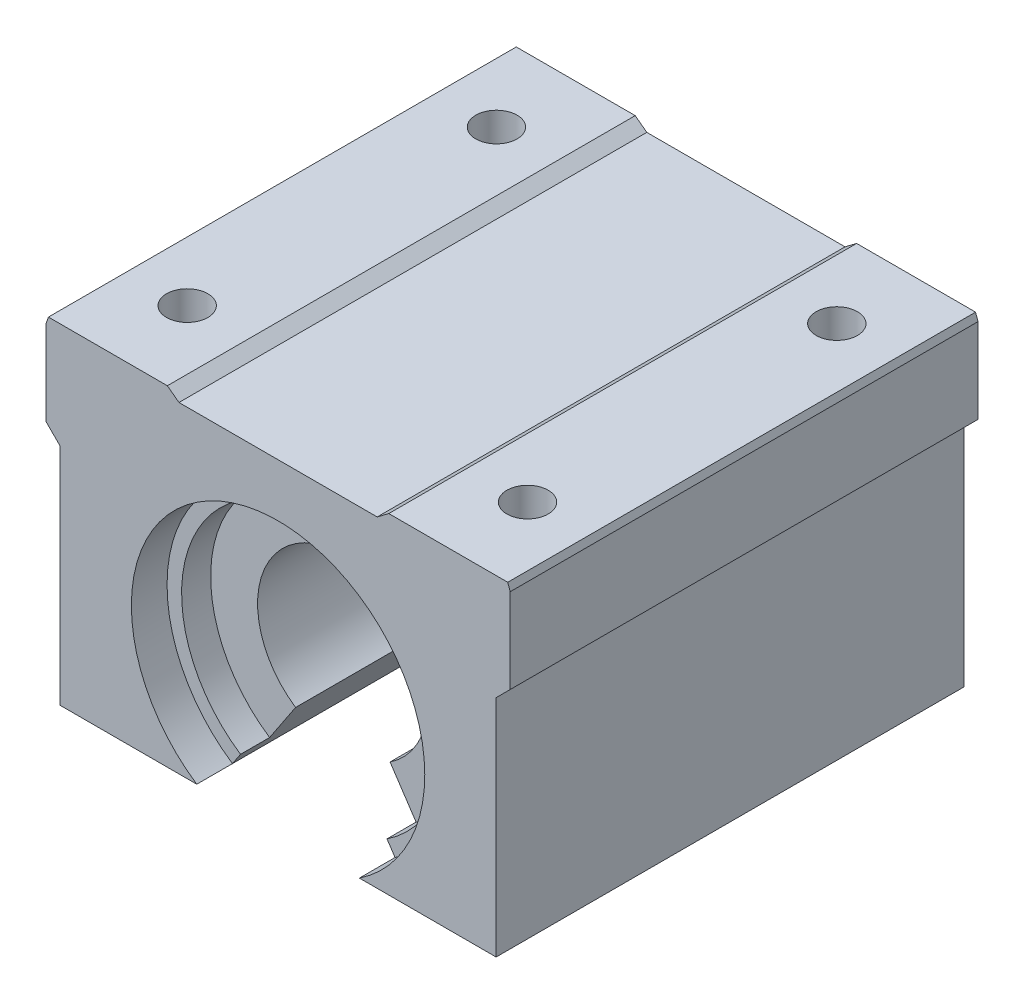
SolidWorks part; units mm, degrees
ref_plane "Front Plane" through (0, 0, 0) normal (0, 0, 1) x (1, 0, 0)
ref_plane "Top Plane" through (0, 0, 0) normal (0, 1, 0) x (1, 0, 0)
ref_plane "Right Plane" through (0, 0, 0) normal (1, 0, 0) x (0, 0, -1)
sketch "Sketch2" plane through (0, 0, 0) normal (0, 0, 1) x (1, 0, 0)
  line L0 (22.0684, 16.2941) -> (10.6384, 16.2941)
  line L1 (10.6384, 16.2941) -> (9.525, 15.4559)
  line L2 (9.525, 15.4559) -> (-9.525, 15.4559)
  line L3 (-9.525, 15.4559) -> (-10.6384, 16.2941)
  line L4 (-10.6384, 16.2941) -> (-22.0684, 16.2941)
  line L5 (-22.3012, 15.6192) -> (-22.3012, 7.4803)
  line L6 (-22.3012, 7.4803) -> (-20.955, 6.1341)
  line L7 (-20.955, 6.1341) -> (-20.955, -15.4559)
  line L8 (-20.955, -15.4559) -> (20.955, -15.4559)
  line L9 (20.955, -15.4559) -> (20.955, 6.1341)
  line L10 (20.955, 6.1341) -> (22.3012, 7.4803)
  line L11 (22.3012, 7.4803) -> (22.3012, 15.6192)
  line L12 (0, -15.4559) -> (0, 15.4559) construction
  line L13 (-22.3012, 15.6192) -> (-22.0684, 16.2941)
  line L14 (22.0684, 16.2941) -> (22.3012, 15.6192)
  dimension "D1" = 31.75
  dimension "D2" = 44.6024
  dimension "D3" = 41.91
  dimension "D4" = 19.05
  dimension "D5" = 11.43
  dimension "D6" = 10.16
  dimension "D7" = 0.8382
extrude "Boss-Extrude1" add sketch "Sketch2" along normal mid plane 44.958
sketch "Sketch3" plane through (0, 16.2941, 0) normal (0, 1, 0) x (1, 0, 0)
  line L0 (-16.3534, 22.479) -> (-16.3534, -22.479) construction
  line L1 (-10.6384, 22.479) -> (-22.0684, 22.479) construction
  line L2 (-10.6384, -22.479) -> (-22.0684, -22.479) construction
  line L3 (16.3534, 22.479) -> (16.3534, -22.479) construction
  line L4 (22.0684, 22.479) -> (10.6384, 22.479) construction
  line L5 (22.0684, -22.479) -> (10.6384, -22.479) construction
  point P0 (-16.3534, 14.859)
  point P1 (16.3534, 14.859)
  point P2 (16.3534, -14.859)
  point P3 (-16.3534, -14.859)
  dimension "D1" = 7.62
  dimension "D2" = 7.62
hole_wizard "5/32 (0.15625) Diameter Hole1" positions "Sketch6" profile "Sketch7" hole size "5/32" standard "ANSI Inch" end condition up to next
sketch "Sketch6" plane through (0, 16.2941, 0) normal (0, 1, 0) x (1, 0, 0)
  point P0 (-16.3534, 14.859)
  point P3 (-16.3534, -14.859)
  point P6 (16.3534, -14.859)
  point P9 (16.3534, 14.859)
sketch "Sketch7" plane through (-16.3534, 16.2941, -14.859) normal (1, 0, 0) x (0, 0, 1)
  line L0 (0, 0) -> (0, 31.75)
  line L1 (0, 31.75) -> (1.9844, 31.75)
  line L2 (1.9844, 31.75) -> (1.9844, 0)
  line L5 (1.9844, 0) -> (0, 0)
  line L11 (0, -6.35) -> (0, 107.95) construction
  dimension "Thru Hole Dia." = 3.9688
  dimension "Thru Hole Depth" = 31.75
sketch "Sketch17" plane through (0, 0, 22.479) normal (0, 0, 1) x (1, 0, 0)
  line L0 (9.525, 15.4559) -> (-9.525, 15.4559) construction
  circle A0 centre (0, -3.7211) radius 14.097
  point P2 (0, 10.3759)
  dimension "D2" = 28.194
  dimension "D1" = 5.08
extrude "Cut-Extrude1" cut sketch "Sketch17" against normal through all both and the other way through all
sketch "Sketch18" plane through (0, 0, 0) normal (0, 0, 1) x (1, 0, 0)
  line L0 (-7.8115, -15.4559) -> (-7.0374, -14.293)
  line L1 (7.0374, -14.293) -> (7.8115, -15.4559)
  arc A0 (7.8115, -15.4559) -> (-7.8115, -15.4559) centre (0, -3.7211) ccw construction
  arc A1 (7.8115, -15.4559) -> (-7.8115, -15.4559) centre (0, -3.7211) ccw
  arc A2 (7.0374, -14.293) -> (-7.0374, -14.293) centre (0, -3.7211) ccw
  dimension "D1" = 25.4
extrude "Boss-Extrude2" add sketch "Sketch18" along normal mid plane 38.1
sketch "Sketch19" plane through (0, 0, 0) normal (0, 0, 1) x (1, 0, 0)
  line L0 (-7.0374, -14.293) -> (-4.5391, -10.54)
  line L1 (7.0374, -14.293) -> (4.5391, -10.54)
  arc A0 (7.0374, -14.293) -> (-7.0374, -14.293) centre (0, -3.7211) ccw construction
  arc A1 (7.0374, -14.293) -> (-7.0374, -14.293) centre (0, -3.7211) ccw
  arc A2 (4.5391, -10.54) -> (-4.5391, -10.54) centre (0, -3.7211) ccw
  dimension "D1" = 16.383
extrude "Boss-Extrude3" add sketch "Sketch19" along normal mid plane 32.512
